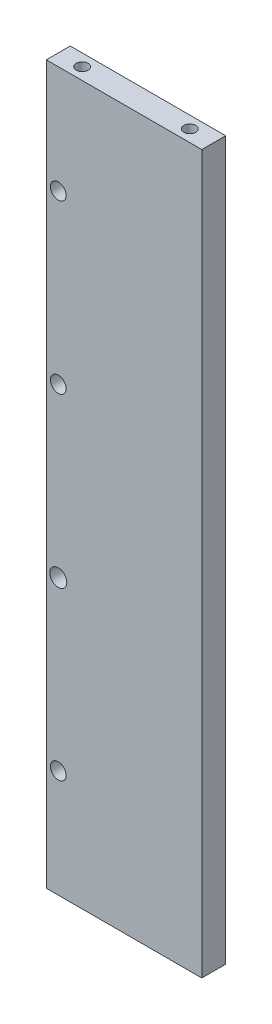
SolidWorks part; units mm, degrees
ref_plane "Front Plane" through (0, 0, 0) normal (0, 0, 1) x (1, 0, 0)
ref_plane "Top Plane" through (0, 0, 0) normal (0, 1, 0) x (1, 0, 0)
ref_plane "Right Plane" through (0, 0, 0) normal (1, 0, 0) x (0, 0, -1)
sketch "Sketch1" plane through (0, 0, 0) normal (0, 0, 1) x (1, 0, 0)
  line L1 (0, 0) -> (65, 0)
  line L2 (0, 0) -> (0, 300)
  line L3 (0, 300) -> (65, 300)
  line L4 (65, 0) -> (65, 300)
  dimension "D1" = 65
  dimension "D2" = 300
extrude "Boss-Extrude1" add sketch "Sketch1" along normal blind 10
sketch "Sketch2" plane through (0, 300, 0) normal (0, 1, 0) x (1, 0, 0)
  line L0 (65, -10) -> (65, 0) construction
  line L1 (0, -10) -> (0, 0) construction
  line L2 (65, 0) -> (0, 0) construction
  circle A0 centre (10, -5) radius 2.5
  circle A1 centre (55, -5) radius 2.5
  point P6 (65, -5)
  point P9 (0, -5)
  dimension "D1" = 5
  dimension "D2" = 5
  dimension "D3" = 10
  dimension "D4" = 10
  dimension "D5" = 5
  dimension "D6" = 5
sketch "Sketch3" plane through (0, 0, 0) normal (0, -1, 0) x (1, 0, 0)
  line L0 (0, 10) -> (0, 0) construction
  line L1 (65, 10) -> (65, 0) construction
  line L3 (0, 0) -> (65, 0) construction
  circle A0 centre (55, 5) radius 2.5
  circle A1 centre (10, 5) radius 2.5
  dimension "D1" = 5
  dimension "D2" = 5
  dimension "D3" = 10
  dimension "D4" = 5
  dimension "D5" = 5
  dimension "D6" = 10
hole_wizard "M6 Tapped Hole1" positions "Sketch6" profile "Sketch5" tap size "M6" standard "ISO"
sketch "Sketch6" plane through (0, 0, 0) normal (0, -1, 0) x (-1, 0, 0)
  point P0 (-55, -5)
  point P3 (-10, -5)
sketch "Sketch5" plane through (55, 0, 5) normal (1, 0, 0) x (0, 0, -1)
  line L0 (0, 0) -> (0, 21.5022)
  line L1 (0, 21.5022) -> (2.5, 20)
  line L2 (2.5, 20) -> (2.5, 0)
  line L5 (2.5, 0) -> (0, 0)
  line L10 (0, 21.5022) -> (-2.5, 20) construction
  line L11 (0, -6.35) -> (0, 107.95) construction
  dimension "Tap Drill Dia." = 5
  dimension "Tap Drill Depth" = 20
  dimension "Drill Angle" = 118
cosmetic thread "Hole Thread1" parameters "D1"=14, "D2"=6
cosmetic thread "Hole Thread2" parameters "D1"=14, "D2"=6
hole_wizard "M6 Tapped Hole2" positions "Sketch7" profile "Sketch8" tap size "M6" standard "ISO"
sketch "Sketch7" plane through (0, 300, 0) normal (0, 1, 0) x (1, 0, 0)
  point P0 (10, -5)
  point P3 (55, -5)
sketch "Sketch8" plane through (10, 300, 5) normal (1, 0, 0) x (0, 0, 1)
  line L0 (0, 0) -> (0, 24.5022)
  line L1 (0, 24.5022) -> (2.5, 23)
  line L2 (2.5, 23) -> (2.5, 0)
  line L5 (2.5, 0) -> (0, 0)
  line L10 (0, 24.5022) -> (-2.5, 23) construction
  line L11 (0, -6.35) -> (0, 107.95) construction
  dimension "Tap Drill Dia." = 5
  dimension "Tap Drill Depth" = 23
  dimension "Drill Angle" = 118
cosmetic thread "Hole Thread3" parameters "D1"=17, "D2"=6
cosmetic thread "Hole Thread4" parameters "D1"=17, "D2"=6
sketch "Sketch9" plane through (0, 0, 10) normal (0, 0, 1) x (1, 0, 0)
  line L0 (65, 300) -> (0, 300) construction
  line L1 (0, 0) -> (65, 0) construction
  line L2 (0, 300) -> (0, 0) construction
  circle A0 centre (5, 255) radius 3.3
  circle A1 centre (5, 185) radius 3.3
  circle A2 centre (5, 45) radius 3.3
  circle A3 centre (5, 115) radius 3.5551
  point P14 (32.5, 0)
  dimension "D7" = 6.6
  dimension "D8" = 6.6
  dimension "D9" = 6.6
  dimension "D1" = 45
  dimension "D2" = 115
  dimension "D3" = 45
  dimension "D4" = 5
  dimension "D5" = 5
  dimension "D6" = 5
  dimension "D10" = 5
  dimension "D11" = 115
extrude "Cut-Extrude1" cut sketch "Sketch9" against normal through all
